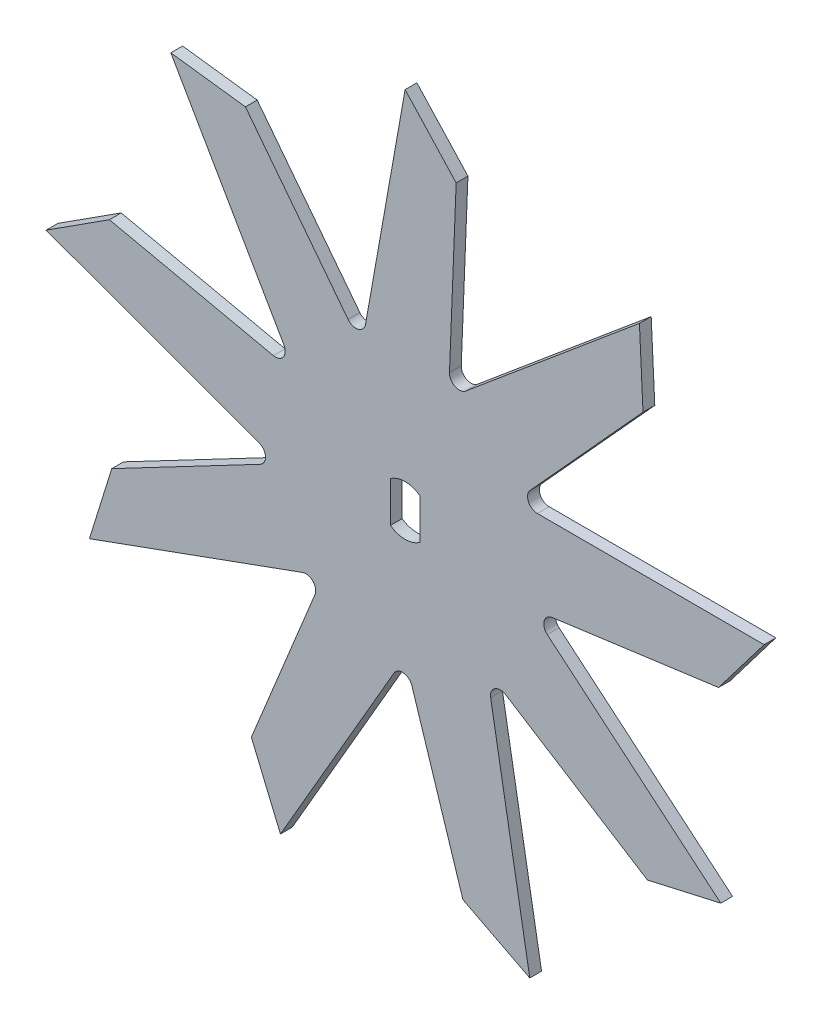
SolidWorks part; units mm, degrees
ref_plane "Plan de face" through (0, 0, 0) normal (0, 0, 1) x (1, 0, 0)
ref_plane "Plan de dessus" through (0, 0, 0) normal (0, 1, 0) x (1, 0, 0)
ref_plane "Plan de droite" through (0, 0, 0) normal (1, 0, 0) x (0, 0, -1)
sketch "Esquisse1" plane through (0, 0, 0) normal (0, 0, 1) x (1, 0, 0)
  line L2 (0, 185.65) -> (0, 0) construction
  line L19 (-7.5, 10.3108) -> (-7.5, -10.3108)
  line L20 (7.5, 10.3108) -> (7.5, -10.3108)
  line L21 (-20.1735, 71.9602) -> (0, 185.65)
  line L22 (22.1458, 60.8451) -> (0, 185.65) construction
  line L23 (0, 185.65) -> (26, 157.5186)
  line L24 (26, 157.5186) -> (22.5955, 72.1249)
  line L25 (119.3335, 142.2162) -> (121.1682, 103.9538)
  line L26 (30.8013, 68.092) -> (119.3335, 142.2162)
  line L27 (121.1682, 103.9538) -> (63.6701, 40.7267)
  line L28 (182.8296, 32.2378) -> (159.6404, 1.7478)
  line L29 (67.3639, 32.3628) -> (182.8296, 32.2378)
  line L30 (159.6404, 1.7478) -> (74.9528, -9.7279)
  line L31 (160.7776, -92.825) -> (123.4151, -101.276)
  line L32 (72.4061, -18.5093) -> (160.7776, -92.825)
  line L33 (123.4151, -101.276) -> (51.1642, -55.6307)
  line L34 (63.496, -174.4539) -> (29.4425, -156.9116)
  line L35 (43.5687, -60.7207) -> (63.496, -174.4539)
  line L36 (29.4425, -156.9116) -> (3.4353, -75.5033)
  line L37 (-63.496, -174.4539) -> (-78.3066, -139.1266)
  line L38 (-5.6549, -74.5202) -> (-63.496, -174.4539)
  line L39 (-78.3066, -139.1266) -> (-45.901, -60.0471)
  line L40 (-160.7776, -92.825) -> (-149.4151, -56.2427)
  line L41 (-52.2326, -53.4509) -> (-160.7776, -92.825)
  line L42 (-149.4151, -56.2427) -> (-73.7597, -16.4942)
  line L43 (-182.8296, 32.2378) -> (-150.6107, 52.9578)
  line L44 (-74.3701, -7.3713) -> (-182.8296, 32.2378)
  line L45 (-150.6107, 52.9578) -> (-67.1055, 34.7766)
  line L46 (-119.3335, 142.2162) -> (-81.3339, 137.3788)
  line L47 (-61.7089, 42.1574) -> (-119.3335, 142.2162)
  line L48 (-81.3339, 137.3788) -> (-29.0518, 69.775)
  circle A0 centre (0, 0) radius 64.75 construction
  circle A1 centre (0, 0) radius 185.65 construction
  arc A11 (-7.5, 10.3108) -> (-7.5, -10.3108) centre (0, 0) ccw construction
  arc A12 (7.5, 10.3108) -> (-7.5, 10.3108) centre (0, 0) ccw
  arc A13 (7.5, -10.3108) -> (7.5, 10.3108) centre (0, 0) ccw construction
  arc A14 (-7.5, -10.3108) -> (7.5, -10.3108) centre (0, 0) ccw
  circle A15 centre (0, 0) radius 159.65 construction
  arc A16 (-67.1055, 34.7766) -> (-61.7089, 42.1574) centre (-66.0418, 39.6621) ccw
  arc A17 (-73.7597, -16.4942) -> (-74.3701, -7.3713) centre (-76.0852, -12.0679) ccw
  arc A18 (-45.901, -60.0471) -> (-52.2326, -53.4509) centre (-50.5276, -58.1512) ccw
  arc A19 (3.4353, -75.5033) -> (-5.6549, -74.5202) centre (-1.3275, -77.0249) ccw
  arc A20 (51.1642, -55.6307) -> (43.5687, -60.7207) centre (48.4937, -59.8578) ccw
  arc A21 (74.9528, -9.7279) -> (72.4061, -18.5093) centre (75.6242, -14.6826) ccw
  arc A22 (63.6701, 40.7267) -> (67.3639, 32.3628) centre (67.3693, 37.3628) ccw
  arc A23 (-20.1735, 71.9602) -> (-29.0518, 69.775) centre (-25.0966, 72.8338) cw
  arc A24 (22.5955, 72.1249) -> (30.8013, 68.092) centre (27.5915, 71.9257) ccw
  point P34 (0, 0)
  point P49 (0, 0)
  point P56 (-22.1458, 60.8451)
extrude "Boss.-Extru.1" add sketch "Esquisse1" along normal blind 6
equation "\"D2@Esquisse1\"=40*1.3"
equation "\"D1@Esquisse1\"=133*1.3"
equation "\"D3@Esquisse1\"=20*1.3"
equation "\"D4@Esquisse1\"=20*1.3"
